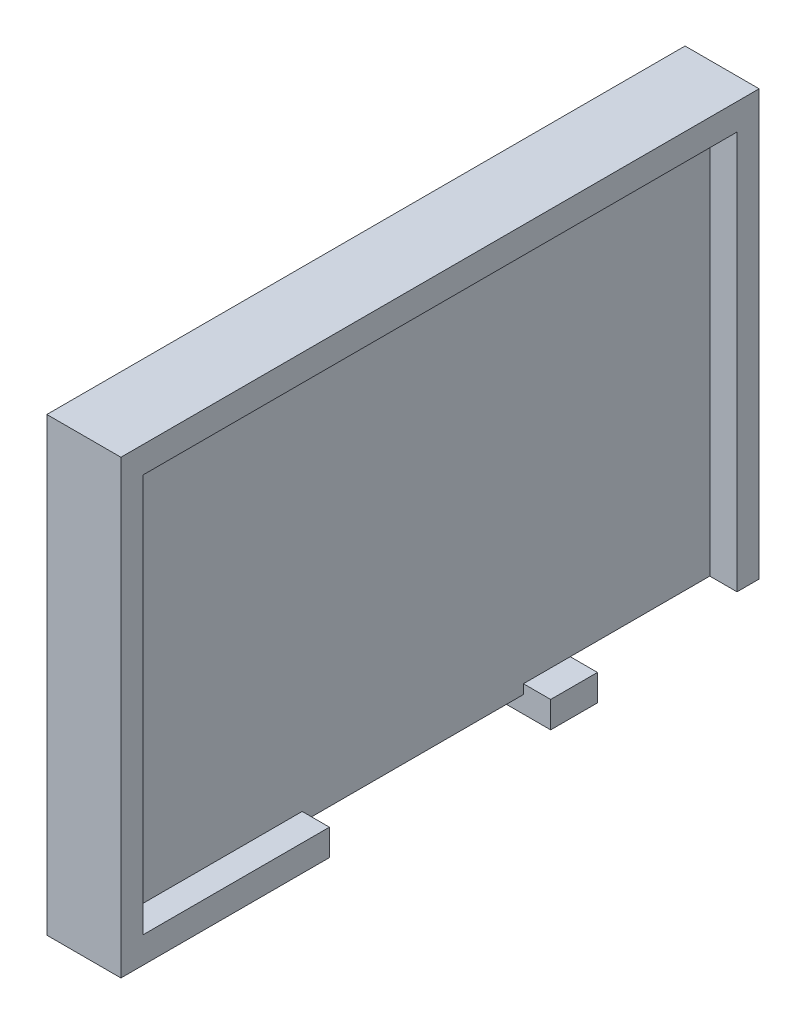
SolidWorks part; units mm, degrees
material "ABS PC"
ref_plane "Front Plane" through (0, 0, 0) normal (1, 0, 0) x (0, 1, 0)
ref_plane "Top Plane" through (0, 0, 0) normal (0, 0, 1) x (0, 1, 0)
ref_plane "Right Plane" through (0, 0, 0) normal (0, 1, 0) x (-1, 0, 0)
sketch "Sketch1" plane through (0, 0, 0) normal (1, 0, 0) x (0, 1, 0)
  line L0 (42.12, 117.43) -> (42.12, 129.18) construction
  line L1 (44.62, 126.68) -> (71.12, 126.68)
  line L2 (44.62, 126.68) -> (44.62, 89.18)
  line L3 (44.62, 89.18) -> (71.12, 89.18)
  line L4 (71.12, 126.68) -> (71.12, 89.18)
  line L5 (42.12, 129.18) -> (89.12, 129.18) construction
  dimension "D1" = 26.5
  dimension "D2" = 37.5
  dimension "D3" = 2.5
  dimension "D4" = 2.5
extrude "Boss-Extrude1" add sketch "Sketch1" along normal blind 4.353 contours L2 L3 L4 L1
sketch "Sketch2" plane through (4.353, 0, 0) normal (1, 0, 0) x (0, 1, 0)
  line L0 (57.87, 126.68) -> (57.87, 89.18)
  line L1 (44.62, 126.68) -> (71.12, 126.68) construction
  line L2 (44.62, 89.18) -> (71.12, 89.18) construction
  line L3 (44.62, 107.93) -> (71.12, 107.93)
  line L4 (44.62, 126.68) -> (44.62, 89.18) construction
  line L5 (71.12, 126.68) -> (71.12, 89.18) construction
  line L7 (69.57, 90.48) -> (46.17, 90.48)
  line L8 (69.57, 90.48) -> (69.57, 125.38)
  line L9 (69.57, 125.38) -> (46.17, 125.38)
  line L10 (46.17, 90.48) -> (46.17, 125.38)
  line L11 (69.57, 90.48) -> (46.17, 125.38) construction
  line L12 (69.57, 125.38) -> (46.17, 90.48) construction
  point P12 (57.87, 107.93)
  dimension "D1" = 23.4
  dimension "D2" = 34.9
extrude "Cut-Extrude1" cut sketch "Sketch2" against normal blind 1.6 contours L7 L10 L9 L8
sketch "Sketch3" plane through (4.353, 0, 0) normal (1, 0, 0) x (0, 1, 0)
  line L0 (44.62, 107.93) -> (46.17, 107.93)
  line L1 (44.62, 126.68) -> (44.62, 89.18) construction
  line L2 (46.17, 90.48) -> (46.17, 125.38) construction
  line L3 (46.17, 125.38) -> (46.17, 126.68)
  line L4 (44.62, 126.68) -> (71.12, 126.68) construction
  line L5 (45.395, 107.93) -> (45.395, 126.68)
  line L7 (46.17, 101.43) -> (44.62, 101.43)
  line L8 (46.17, 101.43) -> (46.17, 114.43)
  line L9 (46.17, 114.43) -> (44.62, 114.43)
  line L10 (44.62, 101.43) -> (44.62, 114.43)
  line L11 (46.17, 101.43) -> (44.62, 114.43) construction
  line L12 (46.17, 114.43) -> (44.62, 101.43) construction
  dimension "D1" = 13
extrude "Cut-Extrude2" cut sketch "Sketch3" against normal blind 1.6 contours L7 L10 L9 L8
sketch "Sketch4" plane through (0, 44.62, 0) normal (0, -1, 0) x (1, 0, 0)
  line L0 (0, 126.68) -> (0, 89.18) construction
  line L1 (2.753, 101.43) -> (0, 101.43)
  line L2 (2.753, 101.43) -> (2.753, 114.43)
  line L3 (2.753, 114.43) -> (0, 114.43)
  line L4 (0, 101.43) -> (0, 114.43)
extrude "Cut-Extrude3" cut sketch "Sketch4" against normal blind 1
sketch "Sketch5" plane through (4.353, 0, 0) normal (1, 0, 0) x (0, 1, 0)
  line L0 (46.17, 90.48) -> (46.17, 101.43) construction
  line L1 (44.62, 89.18) -> (46.17, 89.18)
  line L2 (44.62, 89.18) -> (44.62, 98.68)
  line L3 (44.62, 98.68) -> (46.17, 98.68)
  line L4 (46.17, 89.18) -> (46.17, 98.68)
  dimension "D1" = 9.5
extrude "Cut-Extrude5" cut sketch "Sketch5" against normal blind 1.6 contours L2 L1 L4 L3
sketch "Sketch6" plane through (0, 0, 89.18) normal (0, 0, -1) x (1, 0, 0)
  line L0 (4.353, -46.17) -> (1.953, -46.17)
  line L1 (1.953, -46.17) -> (1.953, -49.12)
  line L2 (1.953, -49.12) -> (0, -49.12)
  line L3 (0, -44.62) -> (0, -71.12) construction
  line L4 (0, -49.12) -> (0, -44.62)
  line L5 (0, -44.62) -> (2.753, -44.62)
  line L6 (2.753, -44.62) -> (2.753, -46.17)
  line M1 (2.753, -46.17) -> (2.753, -44.62)
  line M2 (2.753, -44.62) -> (0, -44.62)
  line M3 (0, -44.62) -> (0, -71.12)
  dimension "D1" = 2.4
  dimension "D2" = 2.95
extrude "Cut-Extrude6" cut sketch "Sketch6" against normal blind 9.5 contours L2 L1 L0 M1 M2 M3
sketch "Sketch7" plane through (0, 0, 0) normal (-1, 0, 0) x (0, -1, 0)
  line L0 (-49.12, 98.68) -> (-49.12, 89.18) construction
  line L1 (-66.8403, 98.7845) -> (-56.9188, 98.7845)
  line L2 (-66.8403, 98.7845) -> (-66.8403, 116.2777)
  line L3 (-66.8403, 116.2777) -> (-56.9188, 116.2777)
  line L4 (-56.9188, 98.7845) -> (-56.9188, 116.2777)
  line L5 (-57.3291, 90.6534) -> (-49.12, 90.6534)
  line L6 (-57.3291, 90.6534) -> (-57.3291, 95.8379)
  line L7 (-57.3291, 95.8379) -> (-49.12, 95.8379)
  line L8 (-49.12, 90.6534) -> (-49.12, 95.8379)
  line L10 (-54.8301, 122.5066) -> (-50.2424, 122.5066)
  line L11 (-54.8301, 122.5066) -> (-54.8301, 95.8379)
  line L12 (-54.8301, 95.8379) -> (-50.2424, 95.8379)
  line L13 (-50.2424, 122.5066) -> (-50.2424, 95.8379)
  line M22 (-49.12, 89.18) -> (-49.12, 98.68)
extrude "Cut-Extrude7" cut sketch "Sketch7" against normal blind 2 contours L13 L10 L11 L7 | L7 L6 L5 M22 | L1 L4 L3 L2
sketch "Sketch8" plane through (0, 0, 0) normal (-1, 0, 0) x (0, -1, 0)
  line L0 (-68.22, 121.18) -> (-68.195, 94.68)
  line L1 (-67.32, 121.18) -> (-69.12, 121.18) construction
  line L2 (-69.095, 94.68) -> (-67.295, 94.68) construction
  line L3 (-68.2075, 107.93) -> (-42.7917, 107.93)
  line L4 (-67.32, 123.18) -> (-47.92, 123.18)
  line L5 (-67.32, 125.18) -> (-67.32, 121.18) construction
  line L6 (-47.92, 121.18) -> (-47.92, 125.18) construction
  line L7 (-57.62, 123.18) -> (-57.62, 84.9383)
  line L8 (-68.22, 121.18) -> (-67.32, 121.18)
  line L9 (-67.32, 121.18) -> (-67.32, 123.18)
  line L10 (-67.42, 121.28) -> (-69.02, 121.28)
  line L11 (-67.32, 121.18) -> (-69.12, 121.18)
  line L12 (-67.32, 121.18) -> (-67.32, 125.18)
  line L13 (-67.32, 125.18) -> (-69.12, 125.18)
  line L14 (-69.12, 121.18) -> (-69.12, 125.18)
  line L15 (-69.02, 121.28) -> (-69.02, 125.08)
  line L16 (-67.42, 125.08) -> (-69.02, 125.08)
  line L17 (-67.42, 121.28) -> (-67.42, 125.08)
  dimension "D1" = 1.8
  dimension "D2" = 4
  dimension "D3" = 0.1
extrude "Boss-Extrude2" add sketch "Sketch8" along normal blind 1.6 contours L10 L17 L16 L15
ref_plane "Plane1" through (0, 57.62, 0) normal (0, -1, 0) x (1, 0, 0)
ref_plane "Plane2" through (0, 0, 107.93) normal (0, 0, -1) x (0, 1, 0)
mirror "Mirror1" about plane through (0, 0, 107.93) normal (0, 0, -1) of "Boss-Extrude2"
mirror "Mirror2" about plane through (0, 57.62, 0) normal (0, -1, 0) of "Boss-Extrude2"
